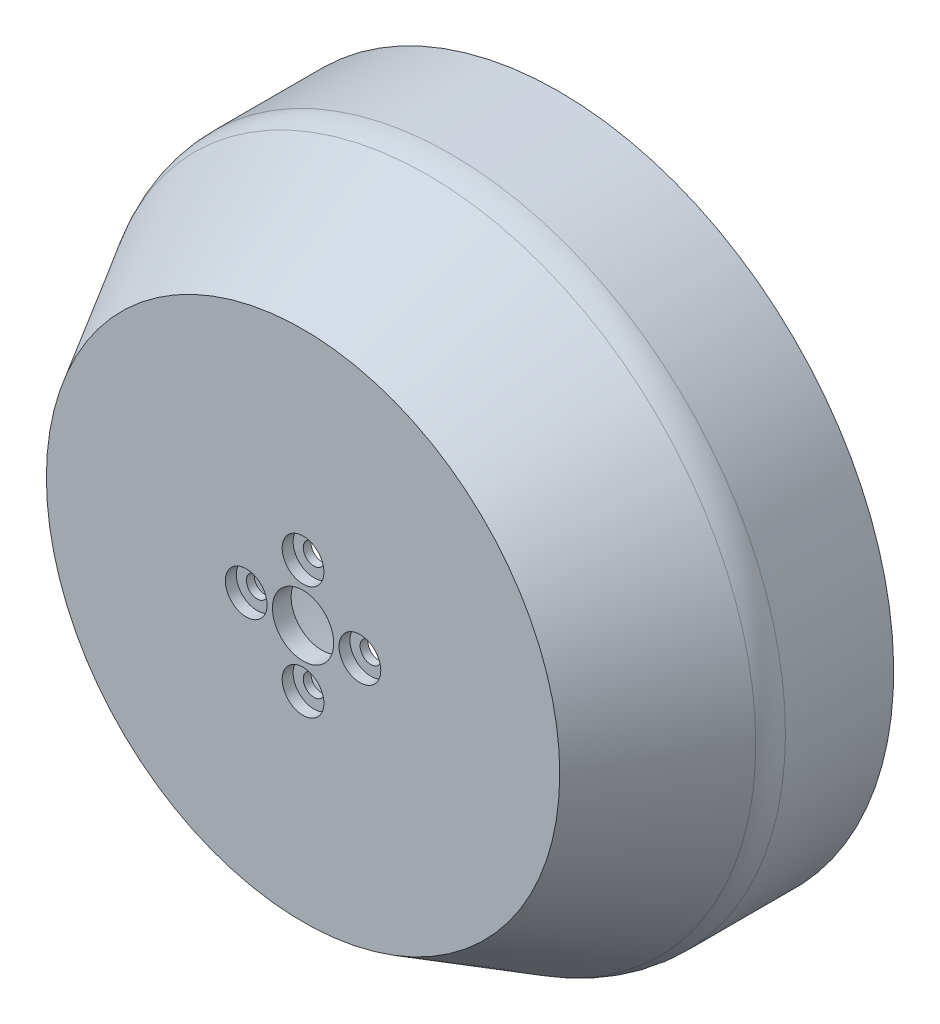
SolidWorks part; units mm, degrees
ref_plane "Front Plane" through (0, 0, 0) normal (0, 0, 1) x (1, 0, 0)
ref_plane "Top Plane" through (0, 0, 0) normal (0, 1, 0) x (1, 0, 0)
ref_plane "Right Plane" through (0, 0, 0) normal (1, 0, 0) x (0, 0, -1)
sketch "Sketch1" plane through (0, 0, 0) normal (0, 0, 1) x (1, 0, 0)
  circle A0 centre (9.62, 10) radius 42.9
  circle A1 centre (9.62, 10) radius 39.5 construction
  dimension "D1" = 3.4
extrude "Boss-Extrude1" add sketch "Sketch1" against normal offset from surface 10 and the other way blind 2.5
chamfer "Chamfer1" distance 10 angle 60 1 edges at (52.52, 10, 2.5)
fillet "Fillet1" radius 6 1 edges at (52.52, 10, -14.8205)
shell "Shell1" thickness 2.4
sketch "Sketch2" plane through (0, 0, 2.5) normal (0, 0, 1) x (1, 0, 0)
  circle A0 centre (9.62, 10) radius 3.925
  circle A1 centre (9.62, 17.285) radius 1.375
  circle A2 centre (9.62, 10) radius 2.925 construction
  circle A3 centre (9.62, 2.715) radius 1.375
  circle A4 centre (2.335, 10) radius 1.375
  circle A5 centre (16.905, 10) radius 1.375
  circle A6 centre (9.62, 2.715) radius 0.875 construction
  dimension "D1" = 1
  dimension "D2" = 0.5
extrude "Cut-Extrude1" cut sketch "Sketch2" against normal up to next
sketch "Sketch3" plane through (0, 0, 2.5) normal (0, 0, 1) x (1, 0, 0)
  line L0 (18.28, 10) -> (19.58, 10) construction
  circle A0 centre (2.335, 10) radius 2.675
  circle A1 centre (9.62, 2.715) radius 2.675
  circle A2 centre (9.62, 17.285) radius 2.675
  circle A3 centre (16.905, 10) radius 2.675
  circle A4 centre (16.905, 10) radius 1.375 construction
  dimension "D1" = 1.3
extrude "Cut-Extrude2" cut sketch "Sketch3" against normal offset from surface (1.4 mm away) 1 up to face at (10.995, 2.715, 0.1)
